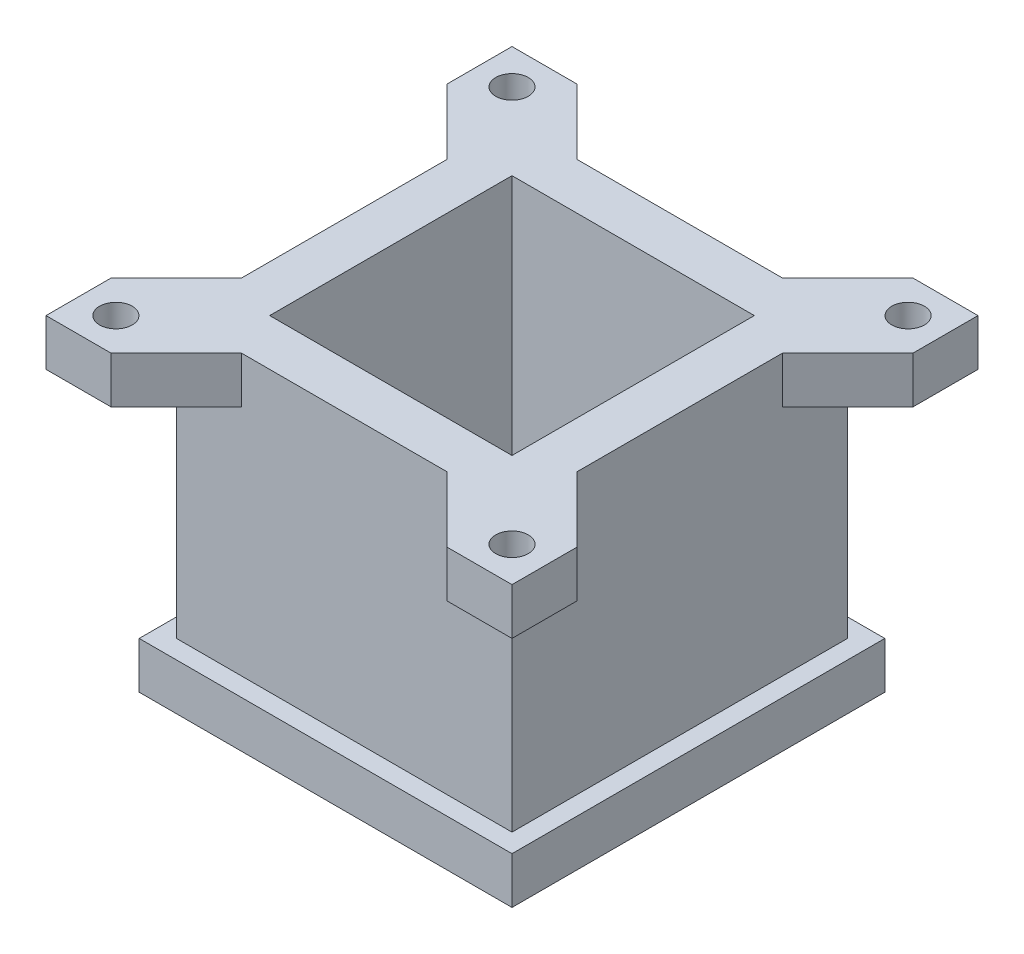
SolidWorks part; units mm, degrees
other "Markup1"
sketch "Sketch5" plane through (-30, 25, 30) normal (-0.0255, 0.5913, 0.806) x (0.9947, 0.0957, -0.0387)
ref_plane "Front Plane" through (0, 0, 0) normal (0, 0, 1) x (1, 0, 0)
ref_plane "Top Plane" through (0, 0, 0) normal (0, 1, 0) x (1, 0, 0)
ref_plane "Right Plane" through (0, 0, 0) normal (1, 0, 0) x (0, 0, -1)
sketch "Sketch1" plane through (0, 0, 0) normal (0, 1, 0) x (1, 0, 0)
  line L1 (13, 13) -> (-13, 13)
  line L2 (13, 13) -> (13, -13)
  line L3 (13, -13) -> (-13, -13)
  line L4 (-13, 13) -> (-13, -13)
  line L5 (13, 13) -> (-13, -13) construction
  line L6 (13, -13) -> (-13, 13) construction
  line L7 (18, -18) -> (-18, -18)
  line L8 (18, -18) -> (18, 18)
  line L9 (18, 18) -> (-18, 18)
  line L10 (-18, -18) -> (-18, 18)
  line L11 (18, -18) -> (-18, 18) construction
  line L12 (18, 18) -> (-18, -18) construction
  point P0 (0, 0)
  point P1 (0, 0)
  dimension "D3" = 26
  dimension "D4" = 26
  dimension "D5" = 36
  dimension "D6" = 36
sketch "Sketch4" plane through (0, 0, 0) normal (0, 1, 0) x (1, 0, 0)
  line L25 (-2.5, -8.525) -> (-2.5, -13)
  line L26 (7.5344, 0) -> (3.7672, 6.525)
  line L31 (3.7672, 6.525) -> (-3.7672, 6.525)
  line L32 (-3.7672, 6.525) -> (-7.5344, 0)
  line L35 (-7.5344, 0) -> (-3.7672, -6.525)
  line L36 (-3.7672, -6.525) -> (3.7672, -6.525)
  line L37 (3.7672, -6.525) -> (7.5344, 0)
  line L42 (13, 13) -> (2.5, 13)
  line L43 (13, 13) -> (13, 2.5)
  line L44 (13, -13) -> (2.5, -13)
  line L51 (-13, 13) -> (-13, 2.5)
  line L52 (13, 13) -> (-13, -13) construction
  line L53 (13, -13) -> (-13, 13) construction
  line L54 (20, 20) -> (-20, 20)
  line L55 (20, 20) -> (20, -20)
  line L56 (20, -20) -> (-20, -20)
  line L57 (-20, 20) -> (-20, -20)
  line L58 (20, 20) -> (-20, -20) construction
  line L59 (20, -20) -> (-20, 20) construction
  line L60 (8.4004, 2.5) -> (4.9219, 8.525)
  line L61 (4.9219, 8.525) -> (2.5, 8.525)
  line L62 (-4.9219, 8.525) -> (-8.4004, 2.5)
  line L63 (-8.4004, -2.5) -> (-4.9219, -8.525)
  line L64 (-4.9219, -8.525) -> (-2.5, -8.525)
  line L65 (4.9219, -8.525) -> (8.4004, -2.5)
  line L66 (2.5, -8.525) -> (2.5, -13)
  line L67 (2.5, -8.525) -> (4.9219, -8.525)
  line L68 (-2.5, -13) -> (-13, -13)
  line L69 (-8.4004, 2.5) -> (-13, 2.5)
  line L70 (-8.4004, -2.5) -> (-13, -2.5)
  line L71 (2.5, 8.525) -> (2.5, 13)
  line L72 (-2.5, 8.525) -> (-2.5, 13)
  line L73 (8.4004, -2.5) -> (13, -2.5)
  line L74 (8.4004, 2.5) -> (13, 2.5)
  line L75 (-2.5, 8.525) -> (-4.9219, 8.525)
  line L76 (-13, -2.5) -> (-13, -13)
  line L77 (13, -2.5) -> (13, -13)
  line L78 (-2.5, 13) -> (-13, 13)
  circle A3 centre (0, 0) radius 6.525 construction
  circle A5 centre (0, 0) radius 8.525 construction
  point P42 (0, 0)
  dimension "D1" = 13.05
  dimension "D2" = 26
  dimension "D7" = 5
  dimension "D3" = 26
  dimension "D4" = 40
  dimension "D5" = 40
  dimension "D6" = 17.05
  dimension "D8" = 2.5
  dimension "D9" = 4
extrude "Boss-Extrude3" add sketch "Sketch4" along normal blind 5
extrude "Boss-Extrude4" add sketch "Sketch1" along normal blind 35
ref_plane "Plane4" through (0, 30, 0) normal (0, 1, 0) x (1, 0, 0)
sketch "Sketch9" plane through (0, 30, 0) normal (0, 1, 0) x (1, 0, 0)
  line L5 (13, 13) -> (-13, 13)
  line L6 (13, 13) -> (13, -13)
  line L7 (25, -25) -> (-25, -25)
  line L8 (25, -25) -> (25, 25)
  line L9 (25, 25) -> (-25, 25)
  line L10 (-25, -25) -> (-25, 25)
  line L11 (25, -25) -> (-25, 25) construction
  line L12 (25, 25) -> (-25, -25) construction
  line L13 (13, -13) -> (-13, -13)
  line L14 (-13, 13) -> (-13, -13)
  line L15 (13, 13) -> (-13, -13) construction
  line L16 (13, -13) -> (-13, 13) construction
  point P0 (0, 0)
  point P1 (0, 0)
  dimension "D1" = 26
  dimension "D2" = 26
  dimension "D3" = 50
  dimension "D4" = 50
extrude "Boss-Extrude6" add sketch "Sketch9" along normal blind 5
ref_plane "Plane5" through (0, 25, 0) normal (0, 1, 0) x (1, 0, 0)
sketch "Sketch10" plane through (0, 25, 0) normal (0, 1, 0) x (1, 0, 0)
  line L0 (-25, 25) -> (-25, -25) construction
  line L1 (25, 25) -> (-25, 25) construction
  circle A6 centre (-21.25, 21.25) radius 1.75
  circle A7 centre (21.25, 21.25) radius 1.75
  circle A8 centre (21.25, -21.25) radius 1.75
  circle A9 centre (-21.25, -21.25) radius 1.75
  point P11 (0, 0)
  dimension "D1" = 3.5
  dimension "D2" = 3.75
  dimension "D3" = 3.75
extrude "Cut-Extrude2" cut sketch "Sketch10" along normal blind 10
sketch "Sketch11" plane through (0, 25, 0) normal (0, 1, 0) x (1, 0, 0)
  line L1 (11, 18) -> (-11, 18)
  line L2 (18, 11) -> (18, -11)
  line L3 (11, -18) -> (-11, -18)
  line L4 (-18, 11) -> (-18, -11)
  line L5 (18, 18) -> (-18, -18) construction
  line L6 (18, -18) -> (-18, 18) construction
  line L7 (-25, 25) -> (-25, -25) construction
  line L8 (-25, -18) -> (-25, 18)
  line L11 (25, 25) -> (-25, 25) construction
  line L12 (-18, 25) -> (18, 25)
  line L14 (25, 18) -> (25, -18)
  line L15 (25, -25) -> (25, 25) construction
  line L17 (18, -25) -> (-18, -25)
  line L18 (-25, -25) -> (25, -25) construction
  line L20 (-25, -18) -> (-18, -11)
  line L22 (18, -25) -> (11, -18)
  line L23 (25, -18) -> (18, -11)
  line L24 (-18, -25) -> (-11, -18)
  line L25 (-25, 18) -> (-18, 11)
  line L26 (-18, 25) -> (-11, 18)
  line L27 (18, 25) -> (11, 18)
  line L28 (25, 18) -> (18, 11)
  point P0 (0, 0)
  dimension "D1" = 36
  dimension "D2" = 36
extrude "Cut-Extrude3" cut sketch "Sketch11" along normal blind 10
equation "\"BallBearingDiameter\" = 22mm"
equation "\"SmallTubeOD\" = 75mm"
equation "\"SmallTubeID\"= \"SmallTubeOD\" - \"WallThickness\" * 2"
equation "\"ZTravel\"= 20mm"
equation "\"WallThickness\"= 5mm"
equation "\"RestrictingFlangeOD\"= \"SmallTubeOD\" + 10mm"
equation "\"D1@Boss-Extrude3\"=\"WallThickness\""
equation "\"HexNutDiameter\" = 13mm"
